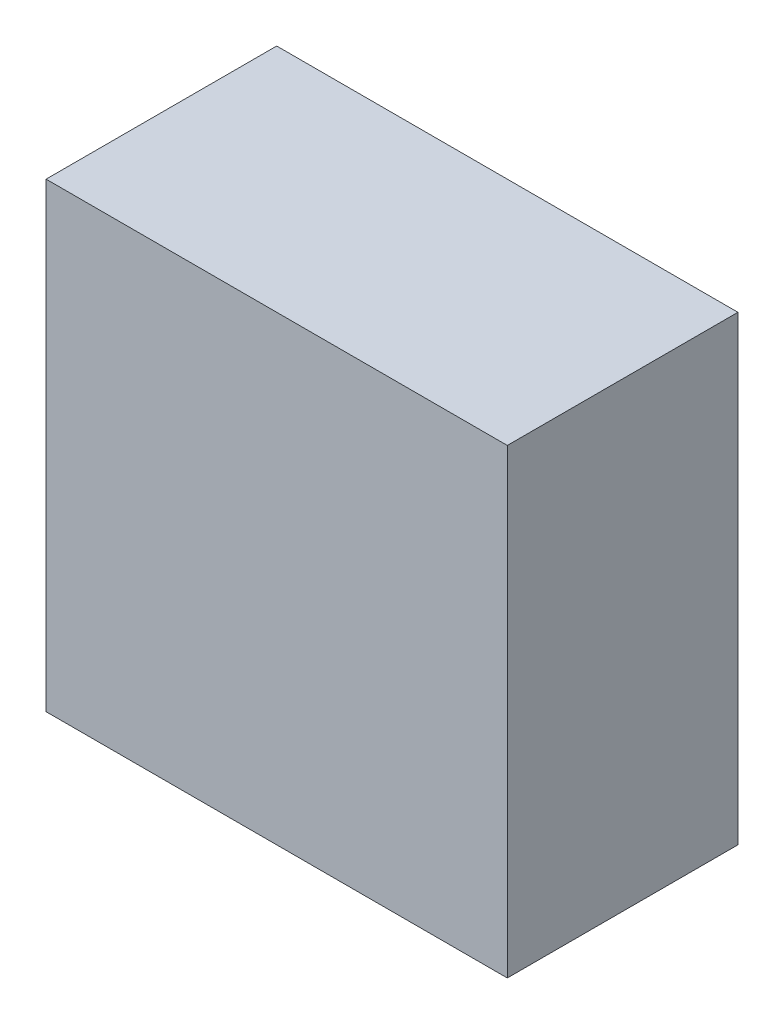
SolidWorks part; units mm, degrees
ref_plane "Front Plane" through (0, 0, 0) normal (0, 0, 1) x (1, 0, 0)
ref_plane "Top Plane" through (0, 0, 0) normal (0, 1, 0) x (1, 0, 0)
ref_plane "Right Plane" through (0, 0, 0) normal (1, 0, 0) x (0, 0, -1)
sketch "Sketch1" plane through (0, 0, 0) normal (0, 1, 0) x (1, 0, 0)
  line L1 (-30, 15) -> (30, 15)
  line L2 (-30, 15) -> (-30, -15)
  line L3 (-30, -15) -> (30, -15)
  line L4 (30, 15) -> (30, -15)
  line L5 (-30, 15) -> (30, -15) construction
  line L6 (-30, -15) -> (30, 15) construction
  point P0 (0, 0)
  dimension "D1" = 30
  dimension "D2" = 60
extrude "Boss-Extrude1" add sketch "Sketch1" along normal blind 60 contours L3 L4 L1 L2
ref_point "Point1"
